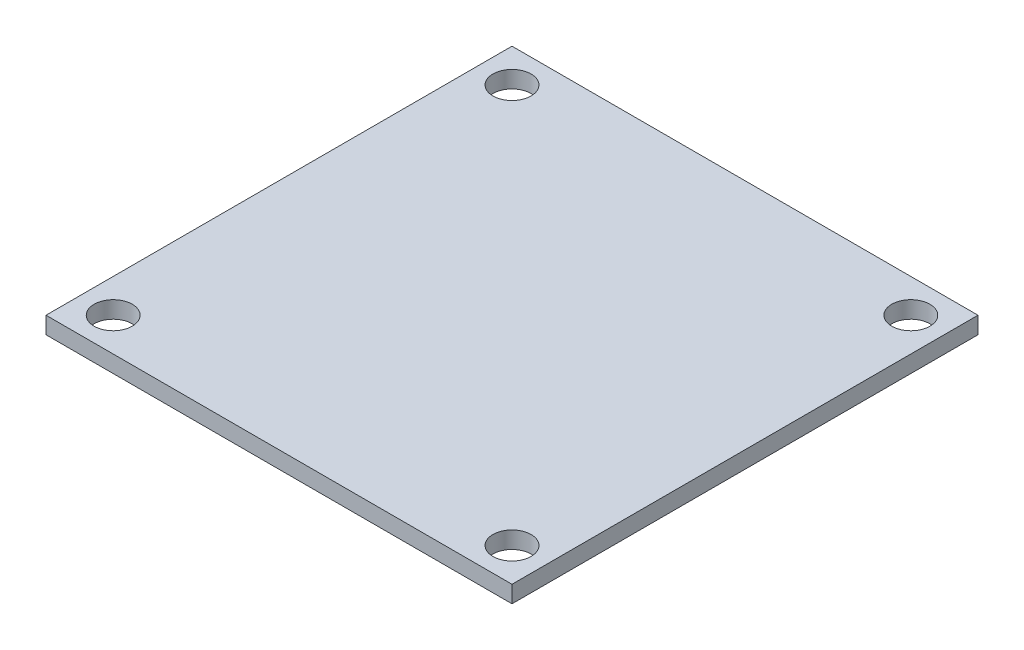
SolidWorks part; units mm, degrees
ref_plane "Front Plane" through (0, 0, 0) normal (0, 0, 1) x (1, 0, 0)
ref_plane "Top Plane" through (0, 0, 0) normal (0, 1, 0) x (1, 0, 0)
ref_plane "Right Plane" through (0, 0, 0) normal (1, 0, 0) x (0, 0, -1)
sketch "Sketch2" plane through (0, 0, 0) normal (0, 1, 0) x (1, 0, 0)
  line L1 (27.5, -27.5) -> (-27.5, -27.5)
  line L2 (27.5, -27.5) -> (27.5, 27.5)
  line L3 (27.5, 27.5) -> (-27.5, 27.5)
  line L4 (-27.5, -27.5) -> (-27.5, 27.5)
  line L5 (27.5, -27.5) -> (-27.5, 27.5) construction
  line L6 (27.5, 27.5) -> (-27.5, -27.5) construction
  point P0 (0, 0)
  dimension "D1" = 55
  dimension "D2" = 55
extrude "Boss-Extrude1" add sketch "Sketch2" along normal blind 2
sketch "Sketch3" plane through (0, 2, 0) normal (0, 1, 0) x (1, 0, 0)
  line L0 (20, -20) -> (23.5355, -23.5355) construction
  line L1 (20, -20) -> (-20, -20) construction
  line L2 (20, -20) -> (20, 20) construction
  line L3 (20, 20) -> (-20, 20) construction
  line L4 (-20, -20) -> (-20, 20) construction
  line L5 (20, -20) -> (-20, 20) construction
  line L6 (20, 20) -> (-20, -20) construction
  line L7 (0, 27.5) -> (0, -27.5) construction
  line L8 (27.5, 27.5) -> (-27.5, 27.5) construction
  line L9 (-27.5, -27.5) -> (27.5, -27.5) construction
  line L10 (27.5, 0) -> (-27.5, 0) construction
  line L11 (27.5, -27.5) -> (27.5, 27.5) construction
  line L12 (-27.5, 27.5) -> (-27.5, -27.5) construction
  circle A0 centre (23.5355, -23.5355) radius 2.25
  circle A1 centre (-23.5355, -23.5355) radius 2.25
  circle A2 centre (23.5355, 23.5355) radius 2.25
  circle A3 centre (-23.5355, 23.5355) radius 2.25
  point P1 (0, 0)
  dimension "D1" = 40
  dimension "D2" = 40
  dimension "D3" = 5
extrude "Cut-Extrude1" cut sketch "Sketch3" against normal blind 2
